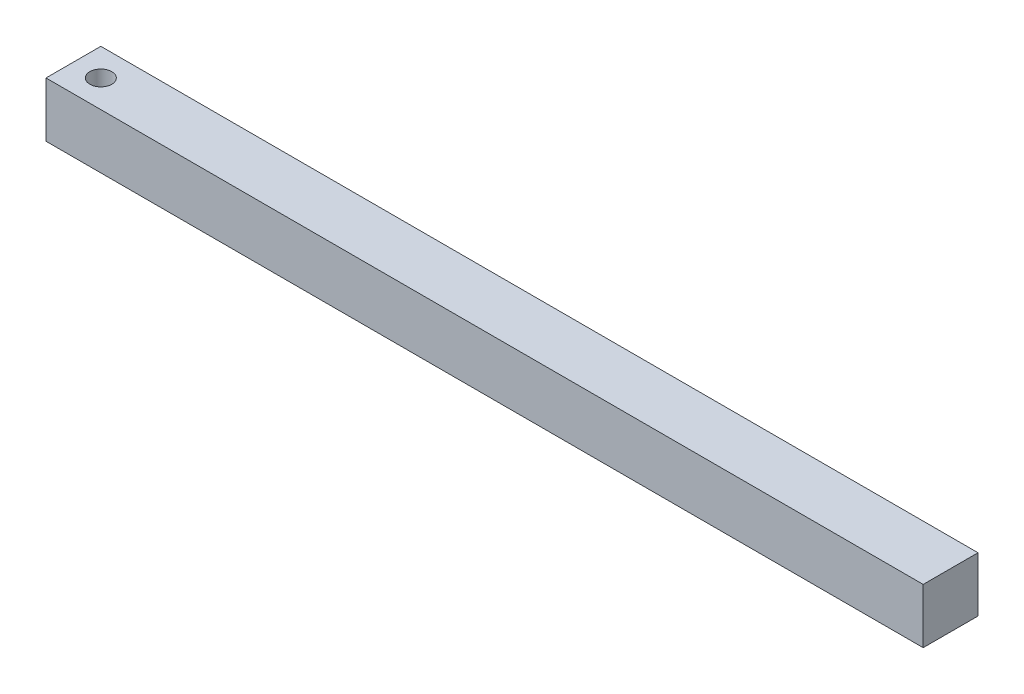
SolidWorks part; units mm, degrees
ref_plane "Front Plane" through (0, 0, 0) normal (0, 0, 1) x (1, 0, 0)
ref_plane "Top Plane" through (0, 0, 0) normal (0, 1, 0) x (1, 0, 0)
ref_plane "Right Plane" through (0, 0, 0) normal (1, 0, 0) x (0, 0, -1)
sketch "Sketch1" plane through (0, 0, 0) normal (0, 1, 0) x (1, 0, 0)
  line L1 (-4.7625, -4.7625) -> (147.6375, -4.7625)
  line L2 (-4.7625, -4.7625) -> (-4.7625, 4.7625)
  line L3 (-4.7625, 4.7625) -> (147.6375, 4.7625)
  line L4 (147.6375, -4.7625) -> (147.6375, 4.7625)
  circle A0 centre (0, 0) radius 1.905
  dimension "D5" = 3.81
  dimension "D1" = 152.4
  dimension "D2" = 9.525
  dimension "D3" = 4.7625
  dimension "D4" = 4.7625
extrude "Boss-Extrude1" add sketch "Sketch1" along normal blind 9.525
equation "\"D3@Sketch1\"=\"D2@Sketch1\"/2"
